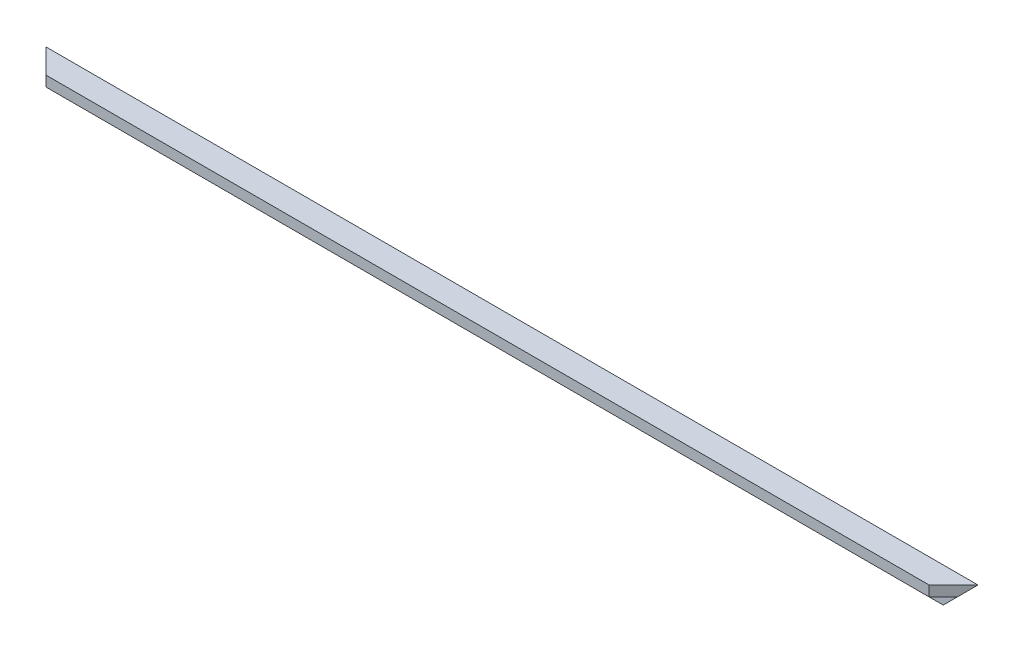
SolidWorks part; units mm, degrees
ref_plane "Plan de face" through (0, 0, 0) normal (0, 0, 1) x (1, 0, 0)
ref_plane "Plan de dessus" through (0, 0, 0) normal (0, 1, 0) x (1, 0, 0)
ref_plane "Plan de droite" through (0, 0, 0) normal (1, 0, 0) x (0, 0, -1)
sketch "Esquisse1" plane through (0, 0, 0) normal (1, 0, 0) x (0, 0, -1)
  line L0 (0, 0) -> (-40, 0)
  line L1 (-40, 0) -> (-40, -17)
  line L2 (-40, -17) -> (-17, -17)
  line L3 (-17, -17) -> (-17, -40)
  line L4 (-17, -40) -> (0, -40)
  line L5 (0, -40) -> (0, 0)
  dimension "D1" = 40
  dimension "D2" = 17
extrude "Boss.-Extru.1" add sketch "Esquisse1" along normal up to vertex (1527 mm away)
sketch "Esquisse2" plane through (0, 0, 0) normal (0, 1, 0) x (1, 0, 0)
  line L0 (1527, 0) -> (1487, -40)
  line L1 (1527, -40) -> (0, -40) construction
  line L2 (1487, -40) -> (1527, -40)
  line L3 (1527, -40) -> (1527, 0)
  line L4 (0, 0) -> (0, -40)
  line L5 (0, -40) -> (40, -40)
  line L6 (40, -40) -> (0, 0)
extrude "Enlèv. mat.-Extru.1" cut sketch "Esquisse2" against normal through all
sketch "Esquisse3" plane through (0, 0, 0) normal (0, 0, -1) x (-1, 0, 0)
  line L0 (-1527, 0) -> (-1487, -40)
  line L1 (-1527, -40) -> (0, -40) construction
  line L2 (-1487, -40) -> (-1527, -40)
  line L3 (-1527, -40) -> (-1527, 0)
  line L4 (-40, -40) -> (0, -40)
  line L5 (0, -40) -> (0, 0)
  line L6 (0, 0) -> (-40, -40)
extrude "Enlèv. mat.-Extru.2" cut sketch "Esquisse3" against normal through all
